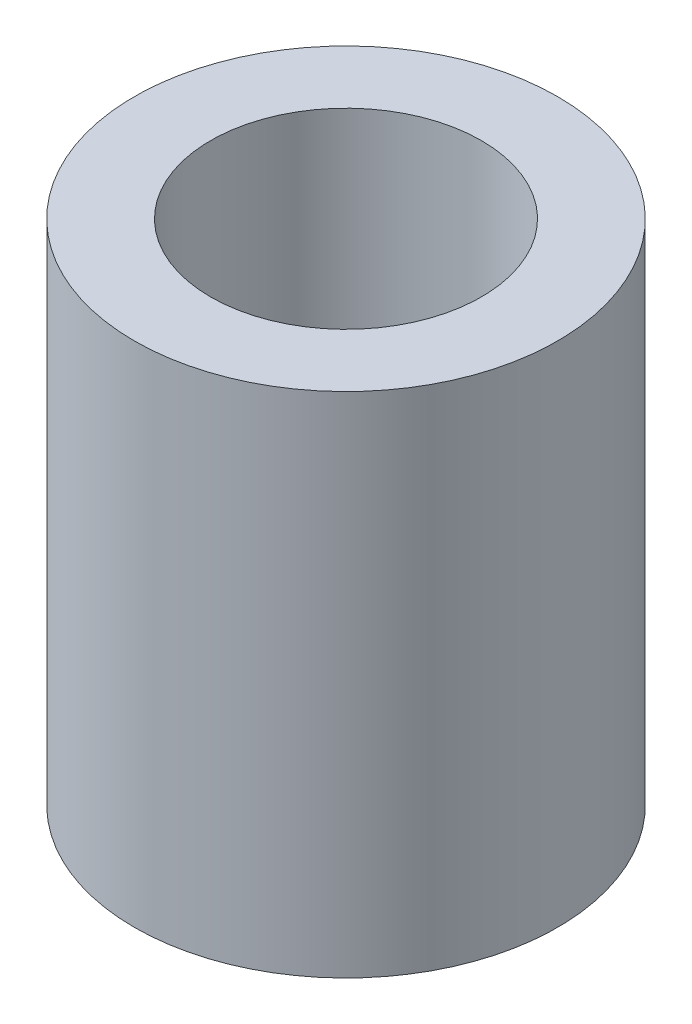
SolidWorks part; units mm, degrees
ref_plane "Front" through (0, 0, 0) normal (0, 0, 1) x (1, 0, 0)
ref_plane "Top" through (0, 0, 0) normal (0, 1, 0) x (1, 0, 0)
ref_plane "Right" through (0, 0, 0) normal (1, 0, 0) x (0, 0, -1)
sketch "Sketch1" plane through (0, 0, 0) normal (0, 1, 0) x (1, 0, 0)
  circle A0 centre (0, 0) radius 2.5
  circle A1 centre (0, 0) radius 1.6
  dimension "D1" = 3.2
  dimension "D2" = 5
extrude "Boss-Extrude1" add sketch "Sketch1" along normal blind 6
